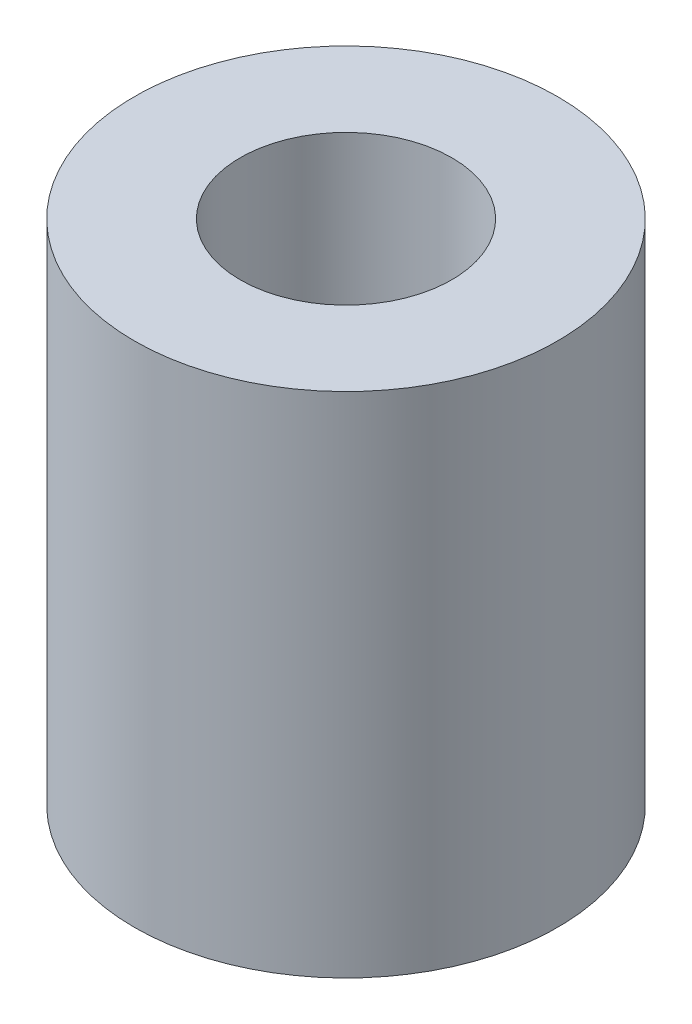
SolidWorks part; units mm, degrees
ref_plane "Front Plane" through (0, 0, 0) normal (0, 0, 1) x (1, 0, 0)
ref_plane "Top Plane" through (0, 0, 0) normal (0, 1, 0) x (1, 0, 0)
ref_plane "Right Plane" through (0, 0, 0) normal (1, 0, 0) x (0, 0, -1)
sketch "Sketch1" plane through (0, 0, 0) normal (0, 1, 0) x (1, 0, 0)
  circle A0 centre (0, 0) radius 1
  circle A1 centre (0, 0) radius 2
  dimension "D1" = 4
  dimension "D2" = 2
extrude "Boss-Extrude1" add sketch "Sketch1" along normal blind 4.8
